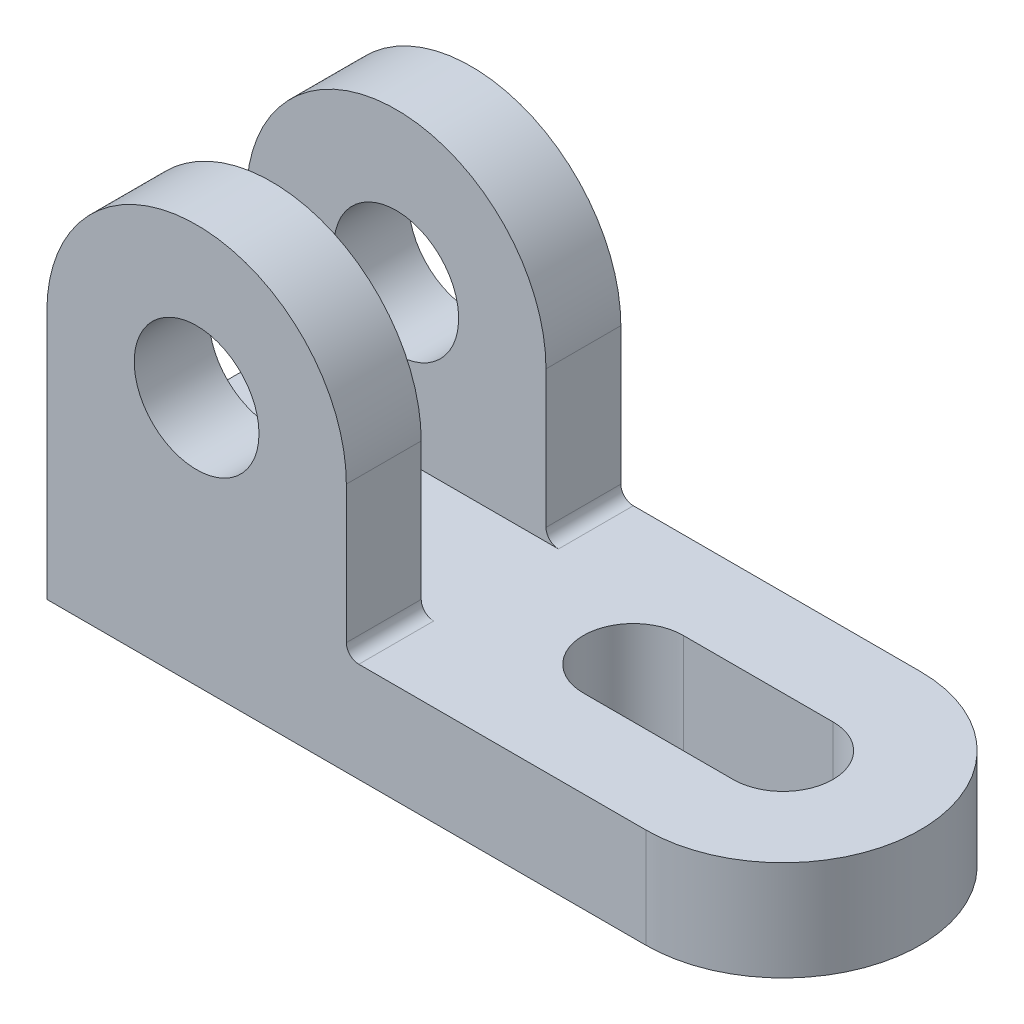
SolidWorks part; units mm, degrees
ref_plane "Front Plane" through (0, 0, 0) normal (0, 0, 1) x (1, 0, 0)
ref_plane "Top Plane" through (0, 0, 0) normal (0, 1, 0) x (1, 0, 0)
ref_plane "Right Plane" through (0, 0, 0) normal (1, 0, 0) x (0, 0, -1)
sketch "Sketch2" plane through (0, 0, 0) normal (0, 1, 0) x (1, 0, 0)
  line L1 (-48, 22) -> (48, 22)
  line L2 (-48, 22) -> (-48, -22)
  line L3 (-48, -22) -> (48, -22)
  arc A0 (48, -22) -> (48, 22) centre (48, 0) ccw
  point P0 (0, 0)
  dimension "D1" = 96
  dimension "D2" = 44
extrude "Boss-Extrude1" add sketch "Sketch2" along normal blind 16
sketch "Sketch3" plane through (0, 16, 0) normal (0, 1, 0) x (1, 0, 0)
  line L0 (48, 0) -> (24, 0) construction
  line L1 (48, -8) -> (24, -8)
  line L2 (48, 8) -> (24, 8)
  arc A0 (48, -8) -> (48, 8) centre (48, 0) ccw
  arc A1 (24, 8) -> (24, -8) centre (24, 0) ccw
  point P4 (36, 0)
  point P9 (0, 0)
extrude "Cut-Extrude2" cut sketch "Sketch3" against normal blind 16
sketch "Sketch5" plane through (0, 0, 22) normal (0, 0, 1) x (1, 0, 0)
  line L0 (-48, 16) -> (-48, 40)
  line L1 (-48, 16) -> (0, 16) construction
  line L2 (-48, 16) -> (48, 16) construction
  line L3 (0, 18) -> (0, 40)
  line L4 (2, 16) -> (21.0559, 16) construction
  arc A0 (0, 40) -> (-48, 40) centre (-24, 40) ccw
  circle A1 centre (-24, 40) radius 10
  arc A2 (2, 16) -> (0, 18) centre (2, 18) cw
  line M7 (48, 16) -> (-48, 16)
  dimension "D1" = 2
extrude "Boss-Extrude3" add sketch "Sketch5" against normal blind 12 contours A2 L3 A0 L0 A1 M7
sketch "Sketch7" plane through (0, 0, -22) normal (0, 0, -1) x (-1, 0, 0)
  line L0 (48, 16) -> (48, 40)
  line L1 (-2, 16) -> (-18.8839, 16) construction
  line L2 (0, 40) -> (0, 18)
  line L3 (-48, 16) -> (48, 16) construction
  arc A0 (48, 40) -> (0, 40) centre (24, 40) ccw
  arc A1 (-2, 16) -> (0, 18) centre (-2, 18) ccw
  circle A2 centre (24, 40) radius 10
  point P14 (0, 16)
  line M4 (48, 16) -> (-48, 16)
  dimension "D1" = 2
extrude "Boss-Extrude4" add sketch "Sketch7" against normal blind 12 contours A1 L0 A0 L2 A2 M4
